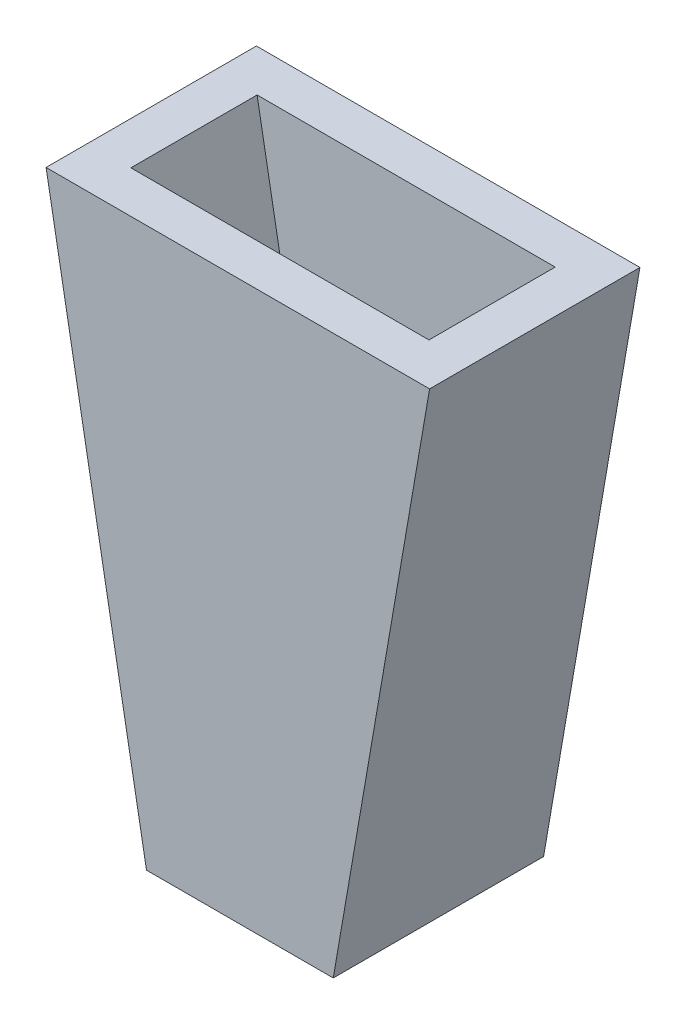
SolidWorks part; units mm, degrees
ref_plane "前视基准面" through (0, 0, 0) normal (0, 0, 1) x (1, 0, 0)
ref_plane "上视基准面" through (0, 0, 0) normal (0, 1, 0) x (1, 0, 0)
ref_plane "右视基准面" through (0, 0, 0) normal (1, 0, 0) x (0, 0, -1)
sketch "草图1" plane through (0, 0, 0) normal (0, 0, 1) x (1, 0, 0)
  line L0 (-15.359, 110) -> (-15.359, 0) construction
  line L1 (-46.859, 110) -> (16.141, 110) construction
  line L2 (-46.859, 0) -> (16.141, 0) construction
  line L3 (-46.859, 55) -> (16.141, 55) construction
  line L7 (-46.859, 110) -> (-46.859, 0) construction
  line L8 (16.141, 110) -> (16.141, 0) construction
  line L9 (-22.1635, 55) -> (-15.359, 55)
  line L10 (-15.359, 55) -> (-8.4877, 55)
  line L11 (-22.1635, 55) -> (-18.5824, 35.09)
  line L12 (-18.5824, 35.09) -> (-11.923, 35.09)
  line L13 (-11.923, 35.09) -> (-8.4877, 55)
  point P17 (-8.4877, 55)
  point P18 (-20.6416, 55)
  point P19 (-22.1635, 55)
extrude "凸台-拉伸1" add sketch "草图1" along normal blind 7.5
shell "抽壳1" thickness 1.5
